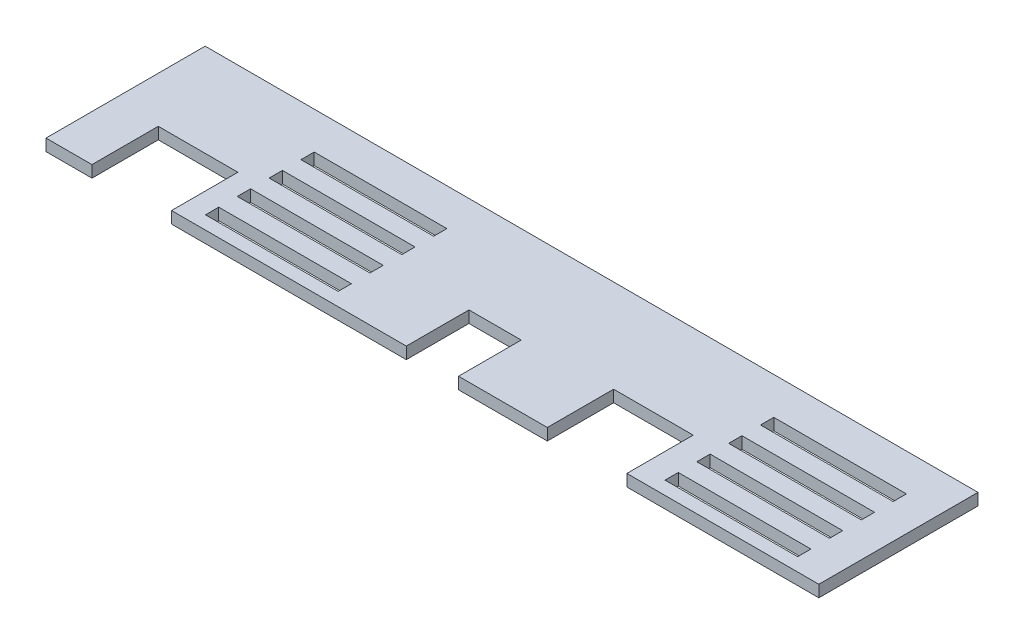
SolidWorks part; units mm, degrees
material "Acrylic (Medium-high impact)"
ref_plane "Front Plane" through (0, 0, 0) normal (0, 0, 1) x (1, 0, 0)
ref_plane "Top Plane" through (0, 0, 0) normal (0, 1, 0) x (1, 0, 0)
ref_plane "Right Plane" through (0, 0, 0) normal (1, 0, 0) x (0, 0, -1)
sketch "Sketch1" plane through (0, 0, 0) normal (0, 1, 0) x (1, 0, 0)
  line L0 (-185, -73.025) -> (185, -73.025)
  line L1 (175, 3.175) -> (-175, 3.175)
  line L2 (-185, -6.825) -> (-185, 3.175)
  line L3 (168.65, -3.175) -> (-168.65, -3.175) construction
  line L4 (-185, 3.175) -> (-175, 3.175)
  line L5 (175, 3.175) -> (185, 3.175)
  line L6 (185, 3.175) -> (185, -6.825)
  line L8 (-185, -6.825) -> (-185, -73.025)
  line L9 (-185, -73.025) -> (-178.65, -73.025) construction
  line L10 (-178.65, -13.175) -> (-178.65, -73.025) construction
  line L12 (185, -6.825) -> (185, -73.025)
  line L13 (185, -73.025) -> (178.65, -73.025) construction
  line L14 (178.65, -13.175) -> (178.65, -73.025) construction
  arc A0 (168.65, -3.175) -> (178.65, -13.175) centre (168.65, -13.175) cw construction
  arc A1 (-168.65, -3.175) -> (-178.65, -13.175) centre (-168.65, -13.175) ccw construction
  point P0 (0, 0)
  point P17 (185, 3.175)
  point P20 (-185, 3.175)
  dimension "D10" = 10
  dimension "D2" = 370
  dimension "D3" = 76.2
  dimension "D4" = 76.2
  dimension "D5" = 185
  dimension "D6" = 3.175
  dimension "D7" = 3.175
  dimension "D8" = 6.35
  dimension "D9" = 6.35
extrude "Boss-Extrude1" add sketch "Sketch1" along normal blind 5.6388
sketch "Sketch2" plane through (0, 5.6388, 0) normal (0, 1, 0) x (1, 0, 0)
  line L9 (-115, -60.325) -> (-51.5, -60.325)
  line L10 (-115, -60.325) -> (-115, -66.675)
  line L11 (-115, -66.675) -> (-51.5, -66.675)
  line L12 (-51.5, -60.325) -> (-51.5, -66.675)
  line L13 (-185, -73.025) -> (185, -73.025) construction
  line L14 (-185, 3.175) -> (-185, -73.025) construction
  dimension "D3" = 6.35
  dimension "D4" = 6.35
  dimension "D5" = 70
  dimension "D6" = 63.5
extrude "Cut-Extrude1" cut sketch "Sketch2" against normal through all
pattern_linear "LPattern1" count 4 spacing 15.24 along (0, 0, -1) count 2 spacing 220 along (1, 0, 0) of "Cut-Extrude1"
sketch "Sketch3" plane through (0, 5.6388, 0) normal (0, 1, 0) x (1, 0, 0)
  line L0 (-185, -73.025) -> (185, -73.025) construction
  line L1 (-12.5, -73.025) -> (12.5, -73.025)
  line L2 (-12.5, -73.025) -> (-12.5, -43.025)
  line L3 (-12.5, -43.025) -> (12.5, -43.025)
  line L4 (12.5, -73.025) -> (12.5, -43.025)
  dimension "D1" = 30
  dimension "D2" = 25
  dimension "D3" = 172.5
extrude "Cut-Extrude2" cut sketch "Sketch3" against normal through all
sketch "Sketch4" plane through (0, 5.6388, 0) normal (0, 1, 0) x (1, 0, 0)
  line L0 (-185, -73.025) -> (-12.5, -73.025) construction
  line L1 (-163, -73.025) -> (-124.9, -73.025)
  line L2 (-163, -73.025) -> (-163, -41.275)
  line L3 (-163, -41.275) -> (-124.9, -41.275)
  line L4 (-124.9, -73.025) -> (-124.9, -41.275)
  line L5 (12.5, -73.025) -> (185, -73.025) construction
  line L6 (55, -73.025) -> (93.1, -73.025)
  line L7 (55, -73.025) -> (55, -41.275)
  line L8 (55, -41.275) -> (93.1, -41.275)
  line L9 (93.1, -73.025) -> (93.1, -41.275)
  line L10 (-185, 3.175) -> (-185, -73.025) construction
  dimension "D1" = 31.75
  dimension "D2" = 31.75
  dimension "D3" = 38.1
  dimension "D4" = 38.1
  dimension "D5" = 22
  dimension "D6" = 240
extrude "Cut-Extrude3" cut sketch "Sketch4" against normal through all
